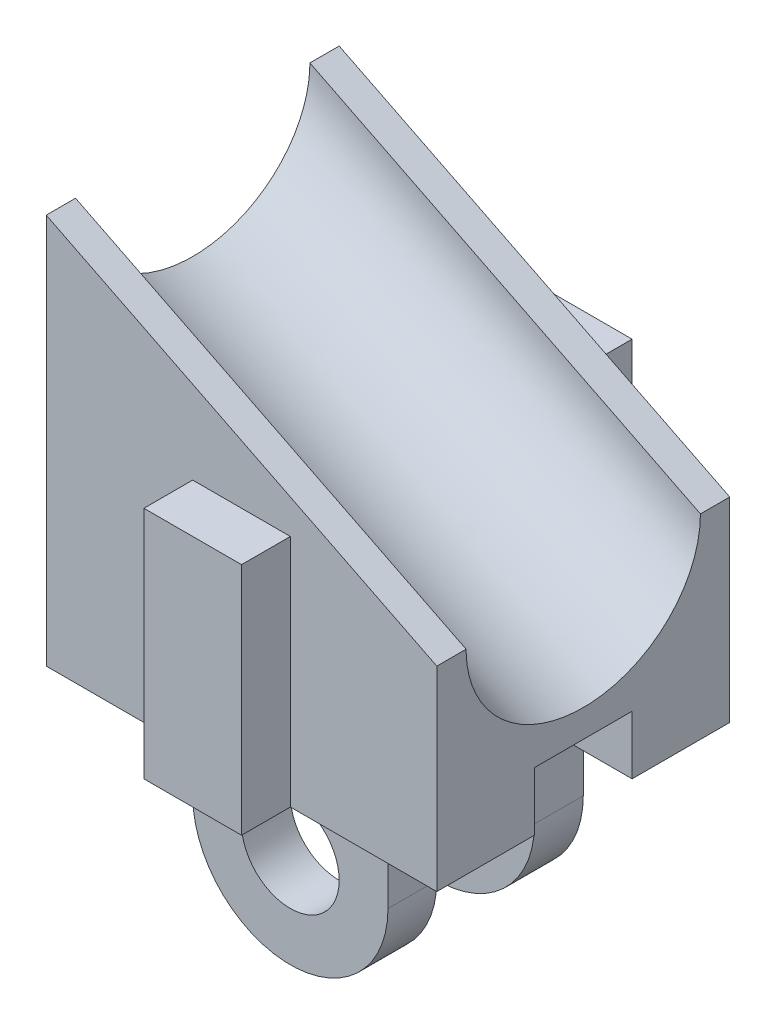
SolidWorks part; units mm, degrees
ref_plane "Front Plane" through (0, 0, 0) normal (0, 0, 1) x (1, 0, 0)
ref_plane "Top Plane" through (0, 0, 0) normal (0, 1, 0) x (1, 0, 0)
ref_plane "Right Plane" through (0, 0, 0) normal (1, 0, 0) x (0, 0, -1)
sketch "Sketch1" plane through (0, 0, 0) normal (0, 0, 1) x (1, 0, 0)
  line L0 (-12.7, 12.7) -> (12.7, 0)
  line L1 (-12.7, -12.7) -> (12.7, -12.7)
  line L2 (-12.7, -12.7) -> (-12.7, 12.7)
  line L4 (12.7, -12.7) -> (12.7, 0)
  point P0 (0, 0)
  point P1 (-12.7, 0)
  point P6 (0, -12.7)
  dimension "D1" = 25.4
  dimension "D2" = 25.4
  dimension "D3" = 12.7
extrude "Boss-Extrude1" add sketch "Sketch1" along normal mid plane 19.05
ref_plane "Plane1" through (-15.24, 7.62, 0) normal (-0.8944, 0.4472, 0) x (0, 0, -1)
sketch "Sketch3" plane through (-15.24, 7.62, 0) normal (-0.8944, 0.4472, 0) x (0, 0, -1)
  line L0 (-9.525, -5.6796) -> (9.525, -5.6796) construction
  ellipse E0 centre (0, -5.6796) end of major axis (7.62, -5.6796) minor radius 6.35
  dimension "D1" = 7.62
  dimension "D2" = 6.35
extrude "Cut-Extrude1" cut sketch "Sketch3" against normal through all
sketch "Sketch4" plane through (0, 0, 9.525) normal (0, 0, 1) x (1, 0, 0)
  line L0 (-12.7, -12.7) -> (12.7, -12.7) construction
  line L1 (-3.175, -12.7) -> (3.175, -12.7)
  line L2 (-3.175, -12.7) -> (-3.175, 2.54)
  line L3 (-3.175, 2.54) -> (3.175, 2.54)
  line L4 (3.175, -12.7) -> (3.175, 2.54)
  line L6 (0, 0) -> (0, -12.7) construction
  point P6 (2.9912, 2.09)
  dimension "D1" = 15.24
  dimension "D2" = 6.35
extrude "Boss-Extrude2" add sketch "Sketch4" along normal blind 3.175
ref_plane "Plane2" through (0, 0, 3.175) normal (0, 0, 1) x (1, 0, 0)
sketch "Sketch5" plane through (0, 0, 3.175) normal (0, 0, 1) x (1, 0, 0)
  line L0 (-6.35, -12.7) -> (-6.35, -18.415)
  line L1 (-12.7, -12.7) -> (-3.175, -12.7) construction
  line L2 (6.35, -12.7) -> (6.35, -18.415)
  line L3 (3.175, -12.7) -> (12.7, -12.7) construction
  line L4 (0, -18.415) -> (0, 0) construction
  line L5 (-6.35, -12.7) -> (6.35, -12.7)
  line L7 (-3.175, -12.7) -> (3.175, -12.7) construction
  arc A0 (-6.35, -18.415) -> (6.35, -18.415) centre (0, -18.415) ccw
  circle A1 centre (0, -18.415) radius 3.175
  dimension "D1" = 3.175
  dimension "D2" = 6.35
  dimension "D3" = 2.54
extrude "Boss-Extrude3" add sketch "Sketch5" along normal blind 3.175
mirror "Mirror1" about plane through (0, 0, 0) normal (0, 0, 1) of "Boss-Extrude3", "Boss-Extrude2"
sketch "Sketch6" plane through (12.7, 0, 0) normal (1, 0, 0) x (0, 0, -1)
  line L0 (3.175, -18.415) -> (3.175, -12.7) construction
  line L1 (-3.175, -12.7) -> (3.175, -12.7)
  line L2 (-3.175, -12.7) -> (-3.175, -8.89)
  line L3 (-3.175, -8.89) -> (3.175, -8.89)
  line L4 (3.175, -12.7) -> (3.175, -8.89)
  dimension "D1" = 3.81
extrude "Cut-Extrude2" cut sketch "Sketch6" against normal up to surface (19.05 mm away) up to face at (-6.35, -15.5575, 4.7625)
